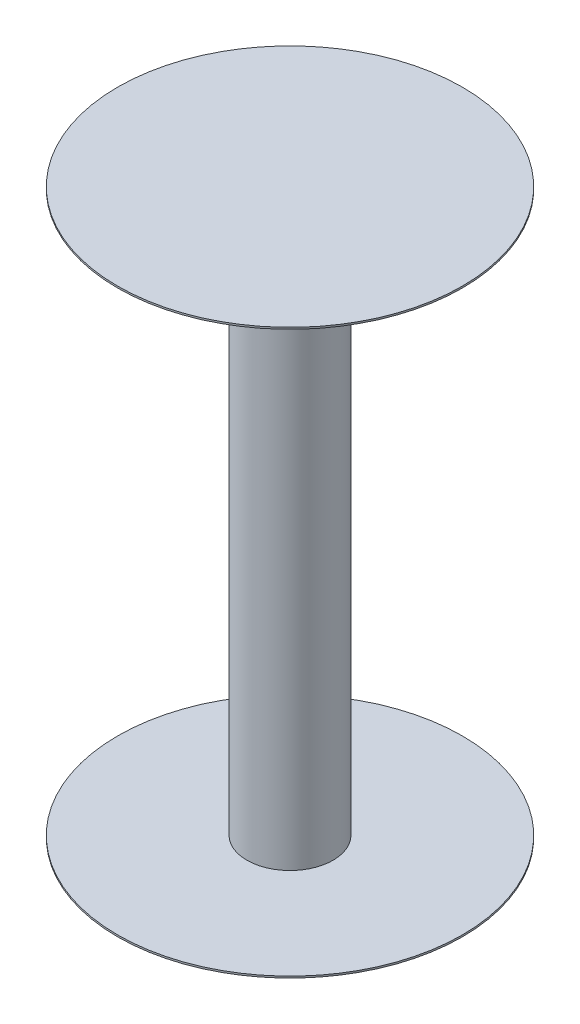
SolidWorks part; units mm, degrees
ref_plane "Front Plane" through (0, 0, 0) normal (0, 0, 1) x (1, 0, 0)
ref_plane "Top Plane" through (0, 0, 0) normal (0, 1, 0) x (1, 0, 0)
ref_plane "Right Plane" through (0, 0, 0) normal (1, 0, 0) x (0, 0, -1)
sketch "Sketch1" plane through (0, 0, 0) normal (0, 1, 0) x (1, 0, 0)
  circle A0 centre (0, 0) radius 12.7
  dimension "D1" = 25.4
extrude "Boss-Extrude1" add sketch "Sketch1" along normal mid plane 165.1
sketch "Sketch2" plane through (0, 82.55, 0) normal (0, 1, 0) x (1, 0, 0)
  circle A0 centre (0, 0) radius 50.8
  dimension "D1" = 101.6
extrude "Boss-Extrude2" add sketch "Sketch2" along normal blind 0.508
mirror "Mirror1" about plane through (0, 0, 0) normal (0, 1, 0) of "Boss-Extrude2"
